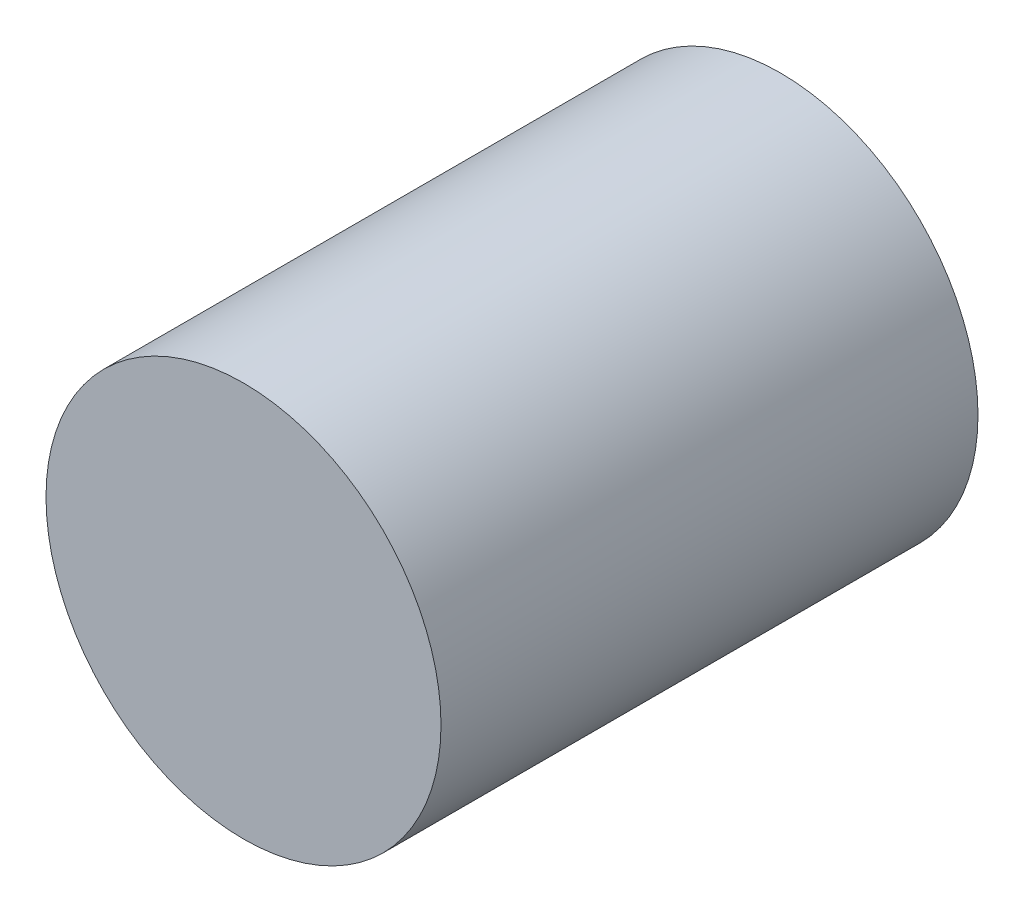
SolidWorks part; units mm, degrees
ref_plane "Front Plane" through (0, 0, 0) normal (0, 0, 1) x (1, 0, 0)
ref_plane "Top Plane" through (0, 0, 0) normal (0, 1, 0) x (1, 0, 0)
ref_plane "Right Plane" through (0, 0, 0) normal (1, 0, 0) x (0, 0, -1)
sketch "Sketch2" plane through (0, 0, 0) normal (0, 0, 1) x (1, 0, 0)
  circle A0 centre (0, 0) radius 21
  dimension "D1" = 42
extrude "Boss-Extrude1" add sketch "Sketch2" along normal blind 57.1
